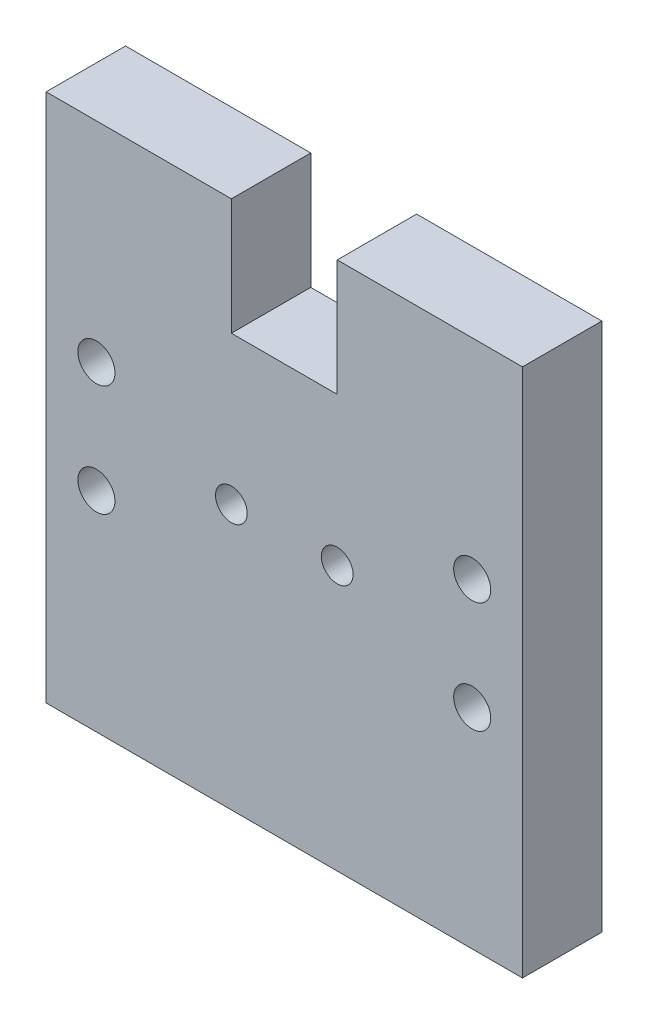
SolidWorks part; units mm, degrees
material "Balsa"
ref_plane "Front Plane" through (0, 0, 0) normal (0, 0, 1) x (1, 0, 0)
ref_plane "Top Plane" through (0, 0, 0) normal (0, 1, 0) x (1, 0, 0)
ref_plane "Right Plane" through (0, 0, 0) normal (1, 0, 0) x (0, 0, -1)
sketch "Sketch1" plane through (0, 0, 0) normal (0, 0, 1) x (1, 0, 0)
  line L0 (250.4184, 126.3335) -> (250.4184, 26.3335) construction
  line L1 (205.4184, 126.3335) -> (295.4184, 126.3335)
  line L2 (205.4184, 126.3335) -> (205.4184, 26.3335)
  line L3 (205.4184, 26.3335) -> (295.4184, 26.3335)
  line L4 (295.4184, 126.3335) -> (295.4184, 26.3335)
  line L5 (205.4184, 76.3335) -> (295.4184, 76.3335) construction
  circle A0 centre (260.4184, 76.3335) radius 3
  circle A1 centre (240.4184, 76.3335) radius 3
  circle A2 centre (214.9184, 86.8335) radius 3.5
  circle A3 centre (214.9184, 65.8335) radius 3.5
  circle A4 centre (285.9184, 86.8335) radius 3.5
  circle A5 centre (285.9184, 65.8335) radius 3.5
  dimension "D3" = 20
  dimension "D1" = 90
  dimension "D2" = 100
extrude "Boss-Extrude1" add sketch "Sketch1" along normal blind 15
sketch "Sketch2" plane through (0, 0, 15) normal (0, 0, 1) x (1, 0, 0)
  line L0 (295.4184, 126.3335) -> (205.4184, 126.3335) construction
  line L1 (240.4184, 126.3335) -> (260.4184, 126.3335)
  line L2 (240.4184, 126.3335) -> (240.4184, 104.3335)
  line L3 (240.4184, 104.3335) -> (260.4184, 104.3335)
  line L4 (260.4184, 126.3335) -> (260.4184, 104.3335)
  line L5 (250.4184, 126.3335) -> (250.4184, 26.3335) construction
  line L6 (205.4184, 26.3335) -> (295.4184, 26.3335) construction
  point P6 (250.4184, 126.3335)
  dimension "D1" = 20
  dimension "D2" = 22
extrude "Cut-Extrude1" cut sketch "Sketch2" against normal blind 15
